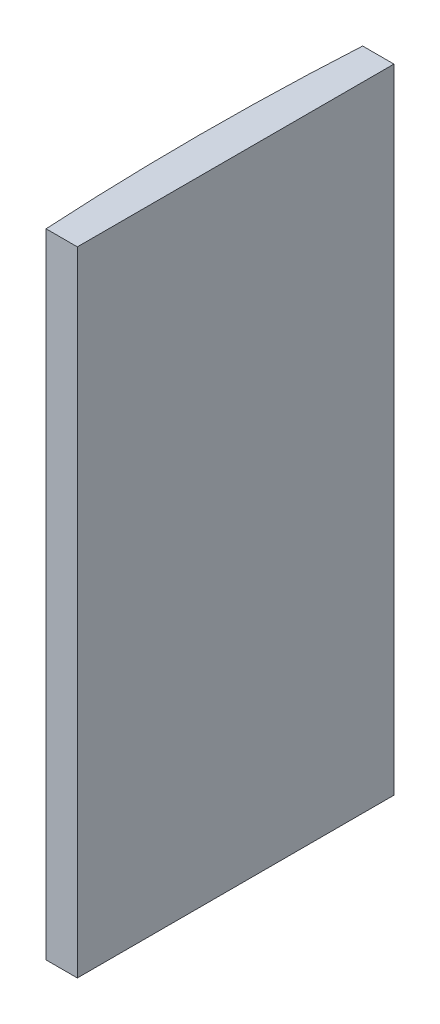
SolidWorks part; units mm, degrees
ref_plane "前视基准面" through (0, 0, 0) normal (0, 0, 1) x (1, 0, 0)
ref_plane "上视基准面" through (0, 0, 0) normal (0, 1, 0) x (1, 0, 0)
ref_plane "右视基准面" through (0, 0, 0) normal (1, 0, 0) x (0, 0, -1)
sketch "草图1" plane through (0, 0, 0) normal (0, 1, 0) x (1, 0, 0)
  line L0 (10.7432, 0) -> (-607.0701, 0) construction
  line L1 (-253.7092, 15) -> (-250.7448, 15)
  line L2 (-253.7092, -15) -> (-250.7448, -15)
  line L3 (-250.7448, 15) -> (-250.7448, -15)
  arc A0 (-253.7092, 15) -> (-253.7092, -15) centre (4.3552, 0) ccw
  point P19 (-254.1448, 0)
  point P20 (-250.7448, 0)
  dimension "D2" = 15
  dimension "D3" = 258.5
  dimension "D4" = 3.4
  dimension "D1" = 15
extrude "凸台-拉伸1" add sketch "草图1" along normal blind 60
